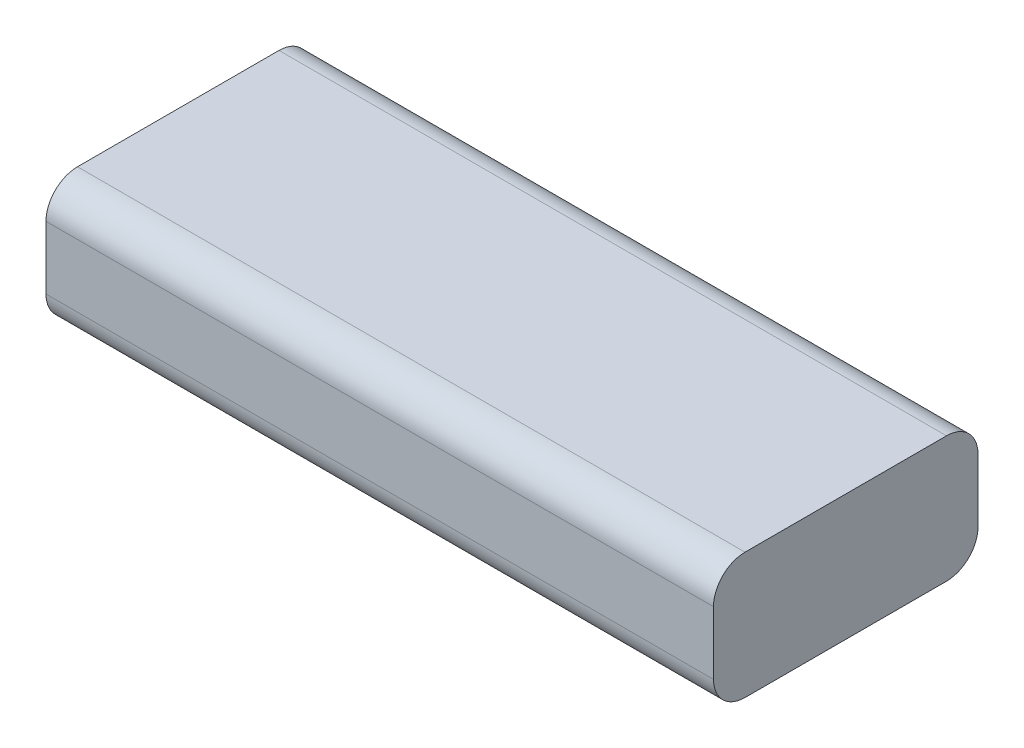
SolidWorks part; units mm, degrees
ref_plane "前视基准面" through (0, 0, 0) normal (0, 0, 1) x (1, 0, 0)
ref_plane "上视基准面" through (0, 0, 0) normal (0, 1, 0) x (1, 0, 0)
ref_plane "右视基准面" through (0, 0, 0) normal (1, 0, 0) x (0, 0, -1)
sketch "草图1" plane through (0, 0, 0) normal (0, 1, 0) x (1, 0, 0)
  line L1 (0, 0) -> (106, 0)
  line L2 (0, 0) -> (0, 42)
  line L3 (0, 42) -> (106, 42)
  line L4 (106, 0) -> (106, 42)
  dimension "D1" = 106
  dimension "D2" = 42
extrude "凸台-拉伸1" add sketch "草图1" along normal blind 20
fillet "圆角1" radius 5 4 edges at (53, 0, -42) (53, 0, 0) (53, 20, -42) (53, 20, 0)
